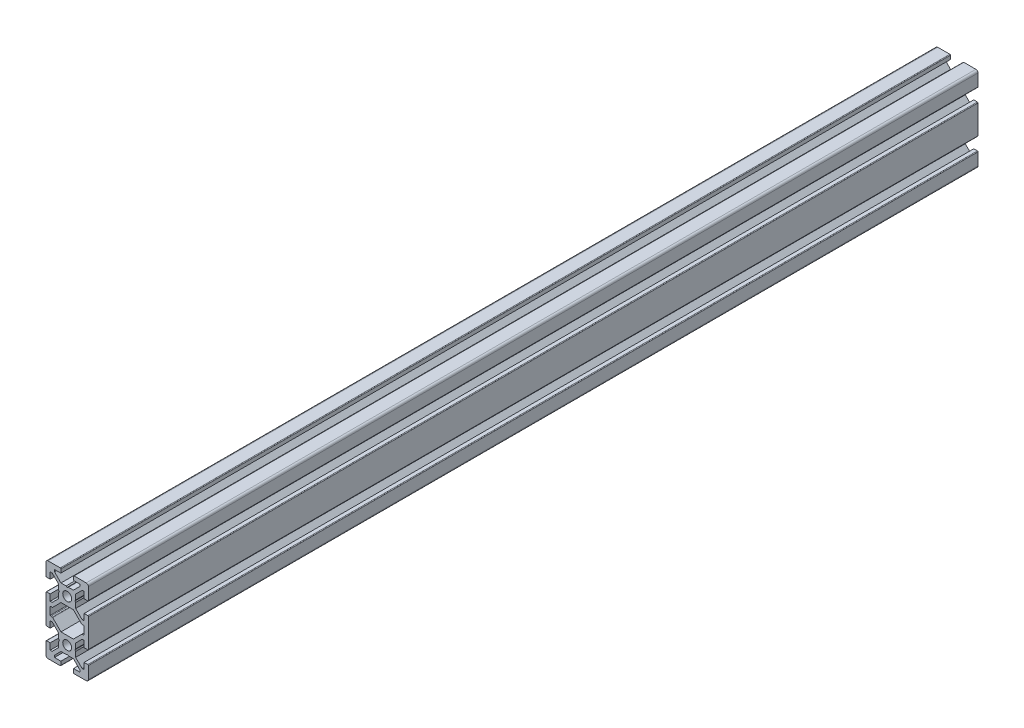
SolidWorks part; units mm, degrees
ref_plane "Front Plane" through (0, 0, 0) normal (0, 0, 1) x (1, 0, 0)
ref_plane "Top Plane" through (0, 0, 0) normal (0, 1, 0) x (1, 0, 0)
ref_plane "Right Plane" through (0, 0, 0) normal (1, 0, 0) x (0, 0, -1)
ref_plane "Plane1" through (0, 0, 0) normal (0, 0, 1) x (1, 0, 0)
sketch "Sketch1" plane through (0, 0, 0) normal (0, 0, 1) x (1, 0, 0)
  line L0 (-10, -13.3) -> (-10, -19)
  line L1 (-9, -20) -> (-3.3, -20)
  line L2 (-3, -19.7) -> (-3, -18)
  line L3 (-3, -18) -> (-6, -18)
  line L4 (-6, -18) -> (-6, -17.0607)
  line L5 (-6, -17.0607) -> (-2.9393, -14)
  line L6 (-2.9393, -14) -> (-0.5196, -14)
  line L7 (-0.5196, -14) -> (0, -13.7)
  line L8 (0, -13.7) -> (0.5196, -14)
  line L9 (0.5196, -14) -> (2.9393, -14)
  line L10 (2.9393, -14) -> (6, -17.0607)
  line L11 (6, -17.0607) -> (6, -18)
  line L12 (6, -18) -> (3, -18)
  line L13 (3, -18) -> (3, -19.7)
  line L14 (3.3, -20) -> (9, -20)
  line L15 (10, -19) -> (10, -13.3)
  line L16 (9.7, -13) -> (8, -13)
  line L17 (8, -13) -> (8, -16)
  line L18 (8, -16) -> (7.0607, -16)
  line L19 (7.0607, -16) -> (4, -12.9393)
  line L20 (4, -12.9393) -> (4, -10.5196)
  line L21 (4, -10.5196) -> (3.7, -10)
  line L22 (3.7, -10) -> (4, -9.4804)
  line L23 (4, -9.4804) -> (4, -7.0607)
  line L24 (4, -7.0607) -> (7.0607, -4)
  line L25 (7.0607, -4) -> (8, -4)
  line L26 (8, -4) -> (8, -7)
  line L27 (8, -7) -> (9.7, -7)
  line L28 (10, -6.7) -> (10, 6.7)
  line L29 (9.7, 7) -> (8, 7)
  line L30 (8, 7) -> (8, 4)
  line L31 (8, 4) -> (7.0607, 4)
  line L32 (7.0607, 4) -> (4, 7.0607)
  line L33 (4, 7.0607) -> (4, 9.4804)
  line L34 (4, 9.4804) -> (3.7, 10)
  line L35 (3.7, 10) -> (4, 10.5196)
  line L36 (4, 10.5196) -> (4, 12.9393)
  line L37 (4, 12.9393) -> (7.0607, 16)
  line L38 (7.0607, 16) -> (8, 16)
  line L39 (8, 16) -> (8, 13)
  line L40 (8, 13) -> (9.7, 13)
  line L41 (10, 13.3) -> (10, 19)
  line L42 (9, 20) -> (3.3, 20)
  line L43 (3, 19.7) -> (3, 18)
  line L44 (3, 18) -> (6, 18)
  line L45 (6, 18) -> (6, 17.0607)
  line L46 (6, 17.0607) -> (2.9394, 14)
  line L47 (2.9394, 14) -> (0.5196, 14)
  line L48 (0.5196, 14) -> (0, 13.7)
  line L49 (0, 13.7) -> (-0.5196, 14)
  line L50 (-0.5196, 14) -> (-2.9393, 14)
  line L51 (-2.9393, 14) -> (-6, 17.0607)
  line L52 (-6, 17.0607) -> (-6, 18)
  line L53 (-6, 18) -> (-3, 18)
  line L54 (-3, 18) -> (-3, 19.7)
  line L55 (-3.3, 20) -> (-9, 20)
  line L56 (-10, 19) -> (-10, 13.3)
  line L57 (-9.7, 13) -> (-8, 13)
  line L58 (-8, 13) -> (-8, 16)
  line L59 (-8, 16) -> (-7.0606, 16)
  line L60 (-7.0606, 16) -> (-4, 12.9394)
  line L61 (-4, 12.9394) -> (-4, 10.5196)
  line L62 (-4, 10.5196) -> (-3.7, 10)
  line L63 (-3.7, 10) -> (-4, 9.4804)
  line L64 (-4, 9.4804) -> (-4, 7.0607)
  line L65 (-4, 7.0607) -> (-7.0607, 4)
  line L66 (-7.0607, 4) -> (-8, 4)
  line L67 (-8, 4) -> (-8, 7)
  line L68 (-8, 7) -> (-9.7, 7)
  line L69 (-10, 6.7) -> (-10, -6.7)
  line L70 (-9.7, -7) -> (-8, -7)
  line L71 (-8, -7) -> (-8, -4)
  line L72 (-8, -4) -> (-7.0607, -4)
  line L73 (-7.0607, -4) -> (-4, -7.0607)
  line L74 (-4, -7.0607) -> (-4, -9.4804)
  line L75 (-4, -9.4804) -> (-3.7, -10)
  line L76 (-3.7, -10) -> (-4, -10.5196)
  line L77 (-4, -10.5196) -> (-4, -12.9394)
  line L78 (-4, -12.9394) -> (-7.0606, -16)
  line L79 (-7.0606, -16) -> (-8, -16)
  line L80 (-8, -16) -> (-8, -13)
  line L81 (-8, -13) -> (-9.7, -13)
  line L82 (-8, 1.7) -> (-8, -1.7)
  line L83 (-7.7, -2) -> (-7.0636, -2)
  line L84 (-6.8515, -2.0879) -> (-2.9393, -6)
  line L85 (-2.9393, -6) -> (2.9393, -6)
  line L86 (2.9393, -6) -> (6.8515, -2.0879)
  line L87 (7.0636, -2) -> (7.7, -2)
  line L88 (8, -1.7) -> (8, 1.7)
  line L89 (7.7, 2) -> (7.0636, 2)
  line L90 (6.8515, 2.0879) -> (2.9393, 6)
  line L91 (2.9393, 6) -> (-2.9393, 6)
  line L92 (-2.9393, 6) -> (-6.8515, 2.0879)
  line L93 (-7.0636, 2) -> (-7.7, 2)
  arc A0 (-10, -19) -> (-9, -20) centre (-9, -19) ccw
  arc A1 (-3.3, -20) -> (-3, -19.7) centre (-3.3, -19.7) ccw
  arc A2 (3, -19.7) -> (3.3, -20) centre (3.3, -19.7) ccw
  arc A3 (9, -20) -> (10, -19) centre (9, -19) ccw
  arc A4 (10, -13.3) -> (9.7, -13) centre (9.7, -13.3) ccw
  arc A5 (9.7, -7) -> (10, -6.7) centre (9.7, -6.7) ccw
  arc A6 (10, 6.7) -> (9.7, 7) centre (9.7, 6.7) ccw
  arc A7 (9.7, 13) -> (10, 13.3) centre (9.7, 13.3) ccw
  arc A8 (10, 19) -> (9, 20) centre (9, 19) ccw
  arc A9 (3.3, 20) -> (3, 19.7) centre (3.3, 19.7) ccw
  arc A10 (-3, 19.7) -> (-3.3, 20) centre (-3.3, 19.7) ccw
  arc A11 (-9, 20) -> (-10, 19) centre (-9, 19) ccw
  arc A12 (-10, 13.3) -> (-9.7, 13) centre (-9.7, 13.3) ccw
  arc A13 (-9.7, 7) -> (-10, 6.7) centre (-9.7, 6.7) ccw
  arc A14 (-10, -6.7) -> (-9.7, -7) centre (-9.7, -6.7) ccw
  arc A15 (-9.7, -13) -> (-10, -13.3) centre (-9.7, -13.3) ccw
  circle A16 centre (0, 10) radius 2.1
  circle A17 centre (0, -10) radius 2.1
  arc A18 (-8, -1.7) -> (-7.7, -2) centre (-7.7, -1.7) ccw
  arc A19 (-7.0636, -2) -> (-6.8515, -2.0879) centre (-7.0635, -2.2999) cw
  arc A20 (6.8515, -2.0879) -> (7.0636, -2) centre (7.0635, -2.2999) cw
  arc A21 (7.7, -2) -> (8, -1.7) centre (7.7, -1.7) ccw
  arc A22 (8, 1.7) -> (7.7, 2) centre (7.7, 1.7) ccw
  arc A23 (7.0636, 2) -> (6.8515, 2.0879) centre (7.0635, 2.2999) cw
  arc A24 (-6.8515, 2.0879) -> (-7.0636, 2) centre (-7.0635, 2.2998) cw
  arc A25 (-7.7, 2) -> (-8, 1.7) centre (-7.7, 1.7) ccw
  dimension "D6" = 4.2
  dimension "D1" = 40
  dimension "D2" = 20
  dimension "D3" = 6
  dimension "D4" = 7
  dimension "D5" = 14
  dimension "D7" = 4
  dimension "D8" = 6
  dimension "D9" = 2
  dimension "D10" = 12
  dimension "D11" = 16
extrude "Boss-Extrude1" add sketch "Sketch1" against normal blind 420
ref_plane "Plane2" through (0, 0, -210) normal (0, 0, 1) x (1, 0, 0)
equation "\"D1@Boss-Extrude1\"=\"ExtrusionLength\""
